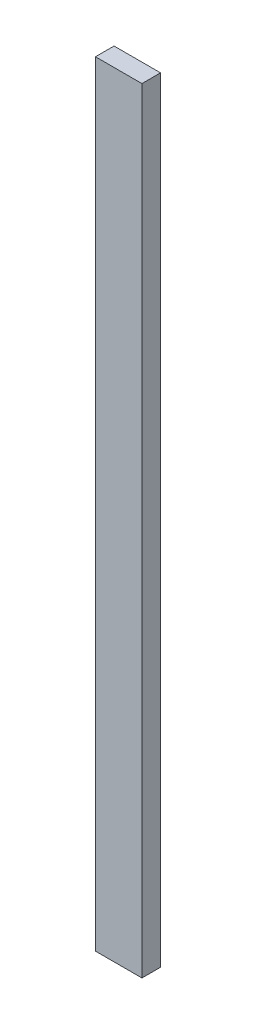
SolidWorks part; units mm, degrees
ref_plane "Plan de face" through (0, 0, 0) normal (0, 0, 1) x (1, 0, 0)
ref_plane "Plan de dessus" through (0, 0, 0) normal (0, 1, 0) x (1, 0, 0)
ref_plane "Plan de droite" through (0, 0, 0) normal (1, 0, 0) x (0, 0, -1)
sketch "Esquisse1" plane through (0, 0, 0) normal (0, 0, 1) x (1, 0, 0)
  line L1 (-7.5, 125) -> (7.5, 125)
  line L2 (-7.5, 125) -> (-7.5, -125)
  line L3 (-7.5, -125) -> (7.5, -125)
  line L4 (7.5, 125) -> (7.5, -125)
  dimension "D1" = 15
  dimension "D2" = 250
  dimension "D3" = 7.5
  dimension "D4" = 125
extrude "Boss.-Extru.1" add sketch "Esquisse1" along normal blind 6
